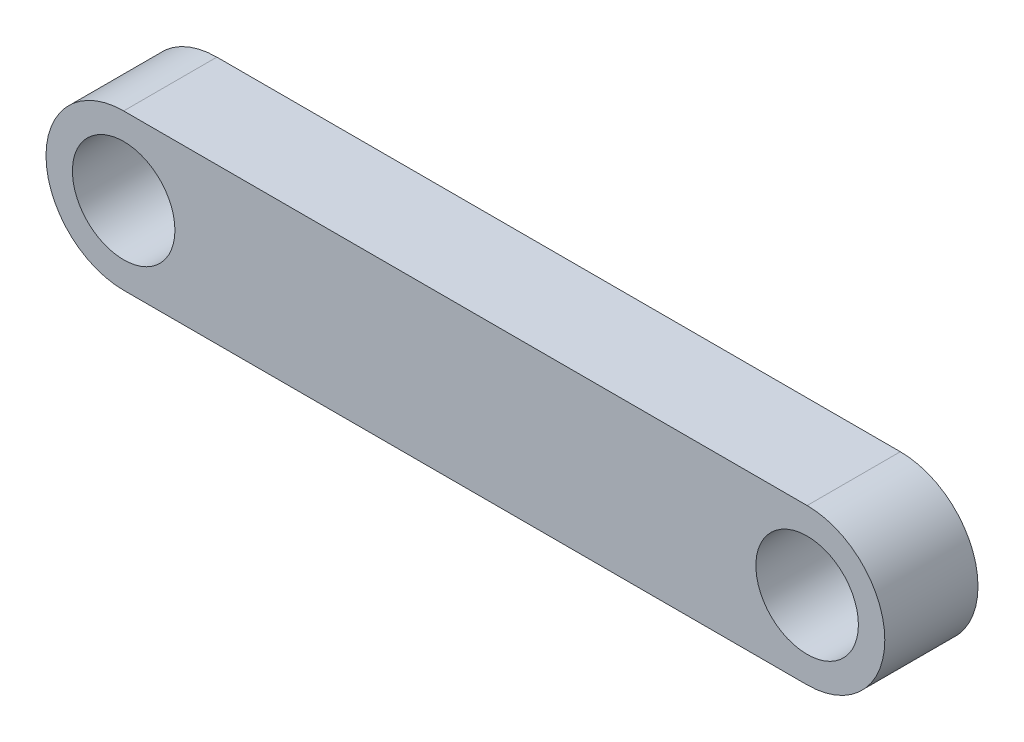
SolidWorks part; units mm, degrees
ref_plane "Front Plane" through (0, 0, 0) normal (0, 0, 1) x (1, 0, 0)
ref_plane "Top Plane" through (0, 0, 0) normal (0, 1, 0) x (1, 0, 0)
ref_plane "Right Plane" through (0, 0, 0) normal (1, 0, 0) x (0, 0, -1)
sketch "Sketch1" plane through (0, 0, 0) normal (0, 0, 1) x (1, 0, 0)
  line L0 (0, 0) -> (22, 0) construction
  line L1 (0, 2.5) -> (22, 2.5)
  line L2 (22, -2.5) -> (0, -2.5)
  circle A0 centre (0, 0) radius 1.65
  circle A1 centre (22, 0) radius 1.65
  arc A2 (0, 2.5) -> (0, -2.5) centre (0, 0) ccw
  arc A3 (22, -2.5) -> (22, 2.5) centre (22, 0) ccw
  dimension "D1" = 3.3
  dimension "D2" = 3.3
  dimension "D3" = 5
  dimension "D4" = 5
  dimension "D5" = 22
extrude "Boss-Extrude1" add sketch "Sketch1" along normal blind 3
